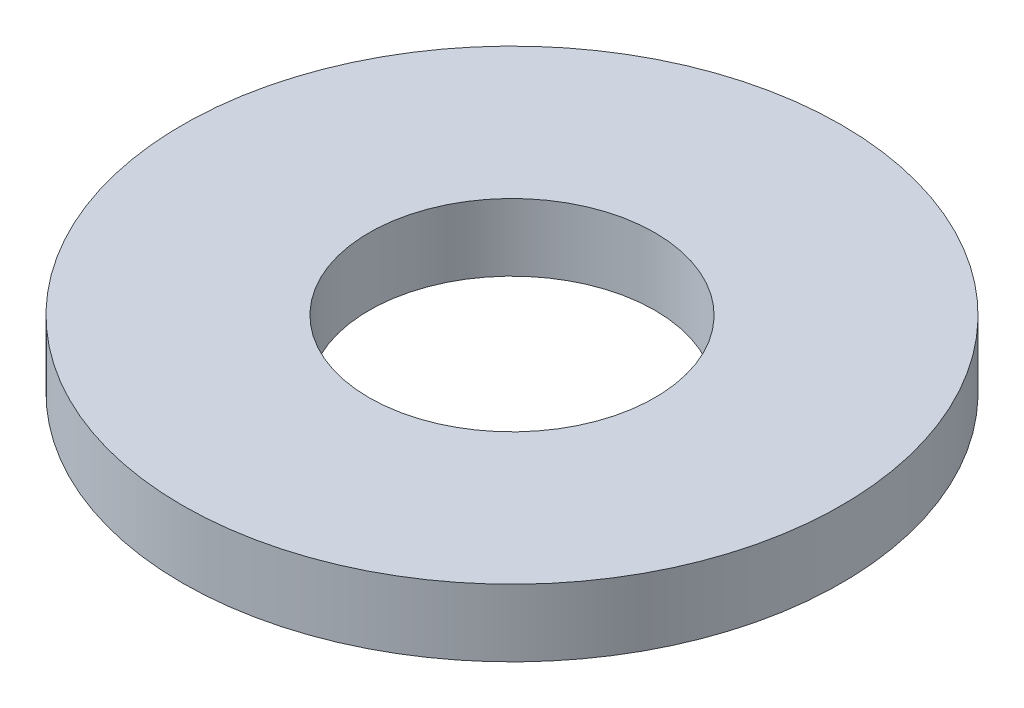
SolidWorks part; units mm, degrees
ref_plane "Front Plane" through (0, 0, 0) normal (0, 0, 1) x (1, 0, 0)
ref_plane "Top Plane" through (0, 0, 0) normal (0, 1, 0) x (1, 0, 0)
ref_plane "Right Plane" through (0, 0, 0) normal (1, 0, 0) x (0, 0, -1)
sketch "Sketch1" plane through (0, 0, 0) normal (0, 1, 0) x (1, 0, 0)
  circle A0 centre (0, 0) radius 9.8
  circle A1 centre (0, 0) radius 4.25
extrude "Boss-Extrude1" add sketch "Sketch1" along normal blind 2
